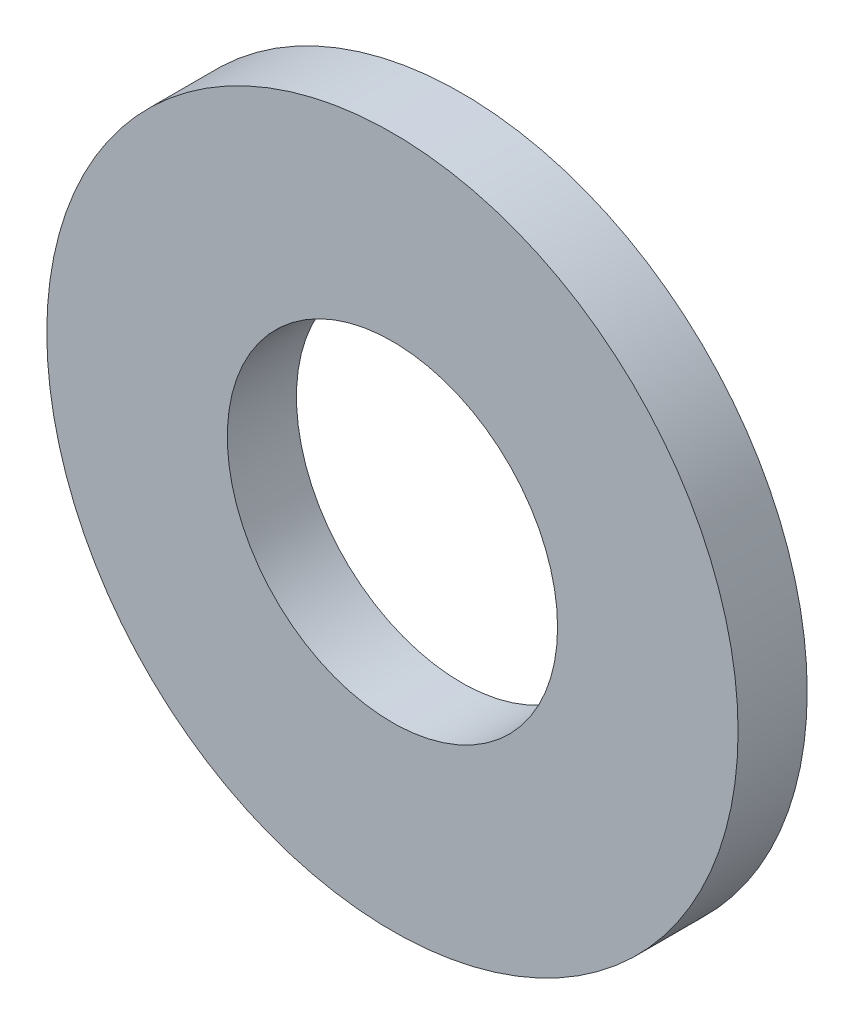
SolidWorks part; units mm, degrees
ref_plane "Front Plane" through (0, 0, 0) normal (0, 0, 1) x (1, 0, 0)
ref_plane "Top Plane" through (0, 0, 0) normal (0, 1, 0) x (1, 0, 0)
ref_plane "Right Plane" through (0, 0, 0) normal (1, 0, 0) x (0, 0, -1)
sketch "Sketch1" plane through (0, 0, 0) normal (0, 0, 1) x (1, 0, 0)
  circle A0 centre (0, 0) radius 4.5
  circle A1 centre (0, 0) radius 2.15
  dimension "OD" = 9
  dimension "ID1" = 4.3
extrude "Boss-Extrude1" add sketch "Sketch1" along normal blind 0.9
